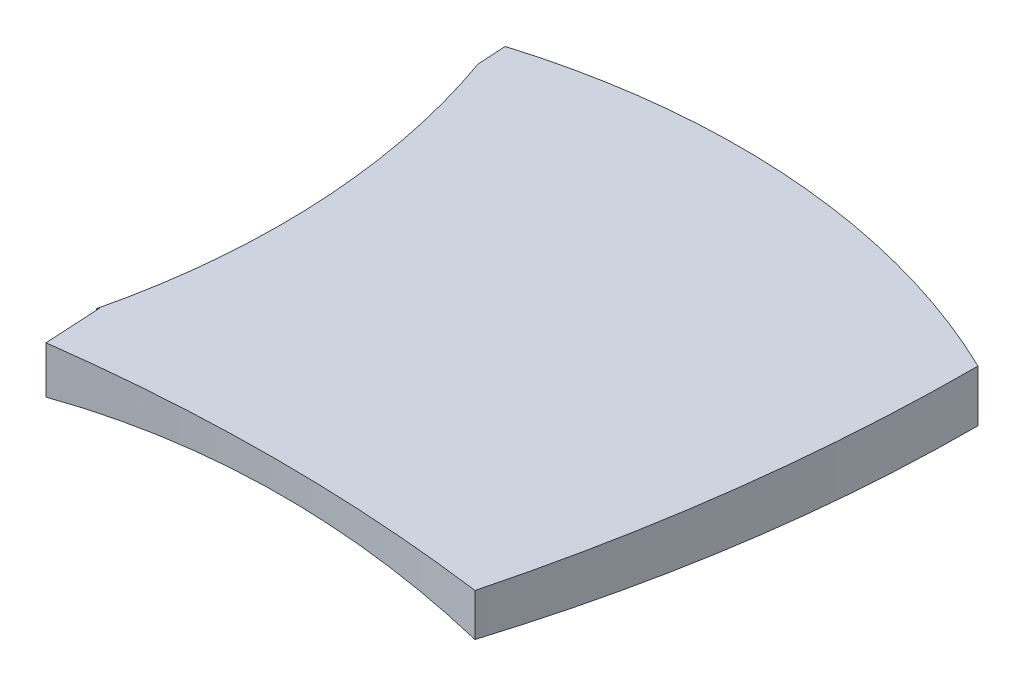
SolidWorks part; units mm, degrees
ref_plane "Front Plane" through (0, 0, 0) normal (0, 0, 1) x (1, 0, 0)
ref_plane "Top Plane" through (0, 0, 0) normal (0, 1, 0) x (1, 0, 0)
ref_plane "Right Plane" through (0, 0, 0) normal (1, 0, 0) x (0, 0, -1)
sketch "Sketch1" plane through (0, 0, 0) normal (0, 1, 0) x (1, 0, 0)
  line L2 (-40, -45) -> (-40.5547, -35.0154)
  line L4 (-2.5, -45) -> (-2.5, -42.5)
  line L6 (-44.7226, 40.0077) -> (-44.4453, 35.0154)
  line L8 (-40.5547, -35.0154) -> (-40.7517, -35.3873)
  arc A0 (-44.4453, 35.0154) -> (-40.7517, -35.3873) centre (-161.5025, -6.4241) cw
  arc A1 (-40, -45) -> (35, -45) centre (-2.5, -325.0801) cw
  arc A2 (45, 32.9423) -> (35, -45) centre (-265.0027, 33.103) cw
  arc A3 (-44.7226, 40.0077) -> (45, 32.9423) centre (-8.8886, -78.161) cw
  point P0 (0, 0)
  point P3 (0, 0)
extrude "Boss-Extrude1" add sketch "Sketch1" along normal blind 15
sketch "Sketch3" plane through (0, 0, 0) normal (0, 0, 1) x (1, 0, 0)
  line L3 (-49.7226, 5) -> (-49.7226, -2.9279)
  line L4 (-49.7226, -2.9279) -> (50, -2.9279)
  line L5 (50, 5) -> (50, -2.9279)
  arc A0 (50, 5) -> (-49.7226, 5) centre (0.1387, -241.1035) ccw
  point P7 (0.1387, 1.036)
extrude "Cut-Extrude2" cut sketch "Sketch3" against normal blind 63 and the other way blind 58
